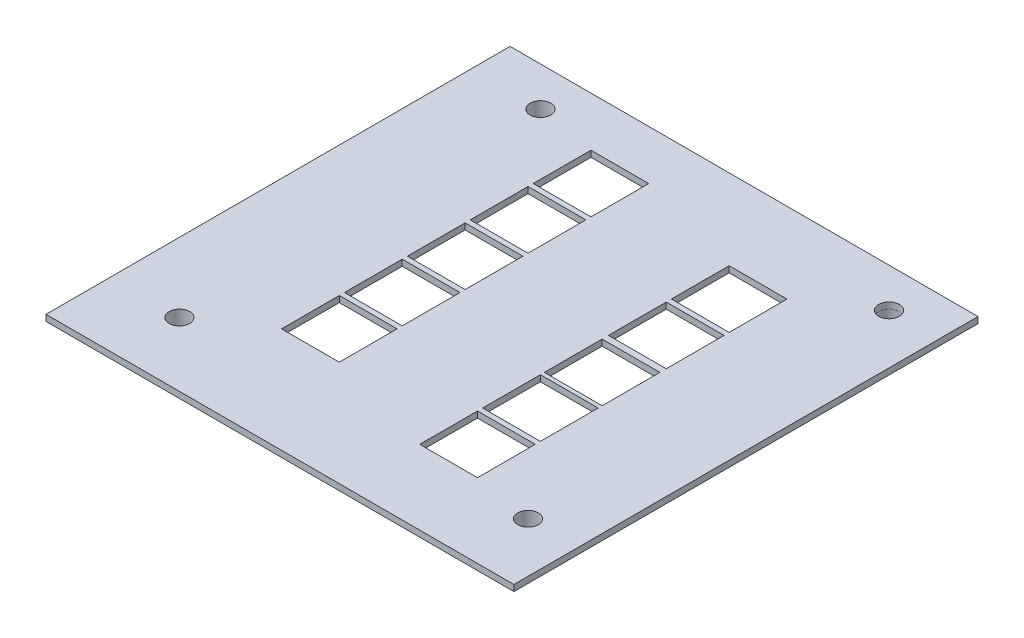
SolidWorks part; units mm, degrees
ref_plane "Спереди" through (0, 0, 0) normal (0, 0, 1) x (1, 0, 0)
ref_plane "Сверху" through (0, 0, 0) normal (0, 1, 0) x (1, 0, 0)
ref_plane "Справа" through (0, 0, 0) normal (1, 0, 0) x (0, 0, -1)
sketch "Эскиз1" plane through (0, 0, 0) normal (0, 1, 0) x (1, 0, 0)
  line L0 (0, 0) -> (45.3694, 0)
  line L1 (45.3694, 0) -> (45.3694, 45)
  line L2 (45.3694, 45) -> (0, 45)
  line L3 (0, 45) -> (0, 0)
  line L5 (12.6378, 34.6025) -> (18.2378, 34.6025)
  line L6 (12.6378, 34.6025) -> (12.6378, 40.2025)
  line L7 (12.6378, 40.2025) -> (18.2378, 40.2025)
  line L8 (18.2378, 34.6025) -> (18.2378, 40.2025)
  line L9 (12.6378, 34.6025) -> (18.2378, 40.2025) construction
  line L10 (12.6378, 40.2025) -> (18.2378, 34.6025) construction
  line L11 (12.6378, 28.5025) -> (18.2378, 28.5025)
  line L12 (12.6378, 28.5025) -> (12.6378, 34.1025)
  line L13 (12.6378, 34.1025) -> (18.2378, 34.1025)
  line L14 (18.2378, 28.5025) -> (18.2378, 34.1025)
  line L15 (12.6378, 28.5025) -> (18.2378, 34.1025) construction
  line L16 (12.6378, 34.1025) -> (18.2378, 28.5025) construction
  line L17 (12.6378, 22.4025) -> (18.2378, 22.4025)
  line L18 (12.6378, 22.4025) -> (12.6378, 28.0025)
  line L19 (12.6378, 28.0025) -> (18.2378, 28.0025)
  line L20 (18.2378, 22.4025) -> (18.2378, 28.0025)
  line L21 (12.6378, 22.4025) -> (18.2378, 28.0025) construction
  line L22 (12.6378, 28.0025) -> (18.2378, 22.4025) construction
  line L23 (12.6378, 16.3025) -> (18.2378, 16.3025)
  line L24 (12.6378, 16.3025) -> (12.6378, 21.9025)
  line L25 (12.6378, 21.9025) -> (18.2378, 21.9025)
  line L26 (18.2378, 16.3025) -> (18.2378, 21.9025)
  line L27 (12.6378, 16.3025) -> (18.2378, 21.9025) construction
  line L28 (12.6378, 21.9025) -> (18.2378, 16.3025) construction
  line L29 (12.6378, 10.2022) -> (18.2378, 10.2022)
  line L30 (12.6378, 10.2022) -> (12.6378, 15.8022)
  line L31 (12.6378, 15.8022) -> (18.2378, 15.8022)
  line L32 (18.2378, 10.2022) -> (18.2378, 15.8022)
  line L33 (12.6378, 10.2022) -> (18.2378, 15.8022) construction
  line L34 (12.6378, 15.8022) -> (18.2378, 10.2022) construction
  line L35 (34.6378, 7.2022) -> (29.0378, 7.2022)
  line L36 (34.6378, 7.2022) -> (34.6378, 12.8022)
  line L37 (34.6378, 12.8022) -> (29.0378, 12.8022)
  line L38 (29.0378, 7.2022) -> (29.0378, 12.8022)
  line L39 (34.6378, 7.2022) -> (29.0378, 12.8022) construction
  line L40 (34.6378, 12.8022) -> (29.0378, 7.2022) construction
  line L41 (34.6378, 13.3022) -> (29.0378, 13.3022)
  line L42 (34.6378, 13.3022) -> (34.6378, 18.9022)
  line L43 (34.6378, 18.9022) -> (29.0378, 18.9022)
  line L44 (-6.0736, 41.2025) -> (53.1705, 41.2025) construction
  line L45 (53.1705, 6.2025) -> (-6.0736, 6.2025) construction
  line L46 (-6.0736, 13.0022) -> (22.9697, 13.0022) construction
  line L47 (22.9697, 19.1025) -> (-6.0736, 19.1025) construction
  line L48 (-6.0736, 25.2025) -> (22.9697, 25.2025) construction
  line L49 (22.9697, 31.3025) -> (-6.0736, 31.3025) construction
  line L50 (23.5485, 37.4025) -> (-6.0736, 37.4025) construction
  line L51 (53.1705, 34.4022) -> (23.5485, 34.4022) construction
  line L52 (53.1705, 28.3022) -> (22.9697, 28.3022) construction
  line L53 (53.1705, 22.2022) -> (23.5485, 22.2022) construction
  line L54 (53.1705, 16.1022) -> (23.5485, 16.1022) construction
  line L55 (53.1705, 10.0022) -> (23.5485, 10.0022) construction
  line L56 (6.7378, 49.2893) -> (6.7378, -5.9561) construction
  line L57 (40.5378, 49.2893) -> (40.5378, -5.8509) construction
  line L58 (15.4378, 49.2893) -> (15.4378, -5.8509) construction
  line L59 (31.8378, 49.2893) -> (31.8378, -5.1143) construction
  line L60 (29.0378, 13.3022) -> (29.0378, 18.9022)
  line L61 (34.6378, 13.3022) -> (29.0378, 18.9022) construction
  line L62 (34.6378, 18.9022) -> (29.0378, 13.3022) construction
  line L63 (34.6378, 19.2875) -> (29.0378, 19.2875)
  line L64 (34.6378, 19.2875) -> (34.6378, 24.8875)
  line L65 (34.6378, 24.8875) -> (29.0378, 24.8875)
  line L66 (29.0378, 19.2875) -> (29.0378, 24.8875)
  line L67 (34.6378, 19.2875) -> (29.0378, 24.8875) construction
  line L68 (34.6378, 24.8875) -> (29.0378, 19.2875) construction
  line L69 (34.6378, 25.5022) -> (29.0378, 25.5022)
  line L70 (34.6378, 25.5022) -> (34.6378, 31.1022)
  line L71 (34.6378, 31.1022) -> (29.0378, 31.1022)
  line L72 (29.0378, 25.5022) -> (29.0378, 31.1022)
  line L73 (34.6378, 25.5022) -> (29.0378, 31.1022) construction
  line L74 (34.6378, 31.1022) -> (29.0378, 25.5022) construction
  line L75 (34.6378, 31.6022) -> (29.0378, 31.6022)
  line L76 (34.6378, 31.6022) -> (34.6378, 37.2022)
  line L77 (34.6378, 37.2022) -> (29.0378, 37.2022)
  line L78 (29.0378, 31.6022) -> (29.0378, 37.2022)
  line L79 (34.6378, 31.6022) -> (29.0378, 37.2022) construction
  line L80 (34.6378, 37.2022) -> (29.0378, 31.6022) construction
  circle A0 centre (6.7378, 41.2025) radius 1
  circle A1 centre (40.5378, 41.2025) radius 1
  circle A2 centre (40.5378, 6.2025) radius 1
  circle A3 centre (6.7378, 6.2025) radius 1
  point P15 (15.4378, 37.4025)
  point P20 (15.4378, 31.3025)
  point P25 (15.4378, 25.2025)
  point P30 (15.4378, 19.1025)
  point P35 (15.4378, 13.0022)
  point P40 (31.8378, 10.0022)
  point P45 (31.8378, 16.1022)
  point P50 (31.8378, 22.0875)
  point P55 (31.8378, 28.3022)
  point P60 (31.8378, 34.4022)
  dimension "D5" = 2
  dimension "D1" = 0
  dimension "D2" = 0
  dimension "D3" = 45
  dimension "D4" = 45.3694
  dimension "D6" = 6.7378
  dimension "D7" = 15.4378
  dimension "D8" = 31.8378
  dimension "D9" = 40.5378
  dimension "D10" = 3.7975
  dimension "D11" = 7.5975
  dimension "D12" = 13.6975
  dimension "D13" = 19.7975
  dimension "D14" = 25.8975
  dimension "D15" = 31.9978
  dimension "D16" = 38.7975
  dimension "D17" = 10.5978
  dimension "D18" = 6.1
  dimension "D19" = 6.1
  dimension "D20" = 6.1
  dimension "D21" = 6.1
  dimension "D22" = 5.6
  dimension "D23" = 5.6
extrude "Бобышка-Вытянуть1" add sketch "Эскиз1" along normal blind 0.6
sketch "Эскиз2" plane through (0, 0, 0) normal (0, -1, 0) x (1, 0, 0)
  circle A0 centre (6.7378, -6.2025) radius 3.5
  circle A1 centre (40.5378, -6.2025) radius 3.5
  circle A2 centre (40.5378, -41.2025) radius 3.5
  circle A3 centre (6.7378, -41.2025) radius 3.5
  circle A4 centre (6.7378, -6.2025) radius 1
  circle A5 centre (40.5378, -6.2025) radius 1
  circle A6 centre (40.5378, -41.2025) radius 0.994
  circle A7 centre (6.7378, -41.2025) radius 1
  dimension "D1" = 7
extrude "Бобышка-Вытянуть2" add sketch "Эскиз2" along normal blind 1
